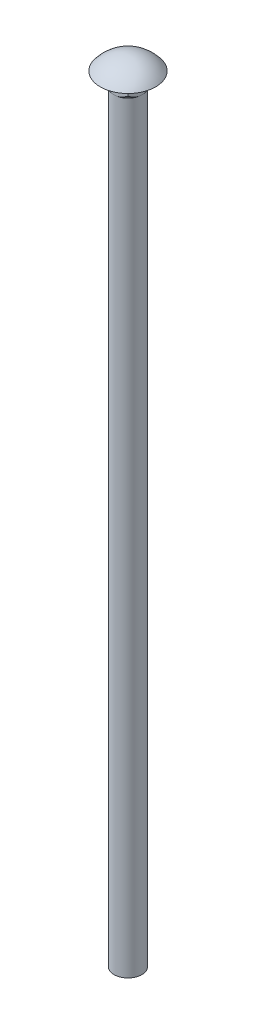
SolidWorks part; units mm, degrees
material "AISI 4340 Steel, annealed"
ref_plane "Front Plane" through (0, 0, 0) normal (0, 0, 1) x (1, 0, 0)
ref_plane "Top Plane" through (0, 0, 0) normal (0, 1, 0) x (1, 0, 0)
ref_plane "Right Plane" through (0, 0, 0) normal (1, 0, 0) x (0, 0, -1)
sketch "Sketch1" plane through (0, 0, 0) normal (0, 1, 0) x (1, 0, 0)
  circle A0 centre (0, 0) radius 6.35
  dimension "D1" = 12.7
extrude "Boss-Extrude1" add sketch "Sketch1" along normal blind 349.25
sketch "Sketch2" plane through (0, 349.25, 0) normal (0, 1, 0) x (1, 0, 0)
  line L1 (-6.35, 6.35) -> (6.35, 6.35)
  line L2 (-6.35, 6.35) -> (-6.35, -6.35)
  line L3 (-6.35, -6.35) -> (6.35, -6.35)
  line L4 (6.35, 6.35) -> (6.35, -6.35)
  dimension "D1" = 12.7
  dimension "D2" = 12.7
  dimension "D3" = 6.35
  dimension "D4" = 6.35
extrude "Boss-Extrude2" add sketch "Sketch2" along normal blind 6.35
sketch "Sketch3" plane through (0, 355.6, 0) normal (0, 1, 0) x (1, 0, 0)
  circle A0 centre (0, 0) radius 12.7
extrude "Boss-Extrude3" add sketch "Sketch3" along normal blind 6.35
sketch "Sketch4" plane through (0, 0, 0) normal (1, 0, 0) x (0, 0, -1)
  line L3 (12.7, 361.95) -> (-12.7, 361.95) construction
  line L4 (-12.7, 355.6) -> (-17.1991, 355.6)
  line L5 (-17.1991, 355.6) -> (-17.1991, 364.4925)
  line L6 (-17.1991, 364.4925) -> (0, 364.4925)
  line L7 (0, 364.4925) -> (0, 361.95)
  line L8 (0, 369.5578) -> (0, 351.1552) construction
  arc A0 (-12.7, 355.6) -> (0, 361.95) centre (0, 346.075) cw
revolve "Cut-Revolve1" cut sketch "Sketch4" angle 360 about L8
sketch "Sketch5" plane through (0, 349.25, 0) normal (0, -1, 0) x (1, 0, 0)
  circle A0 centre (0, 0) radius 6.35
extrude "Cut-Extrude1" cut sketch "Sketch5" against normal blind 6.35 draft 45 flip side to cut
